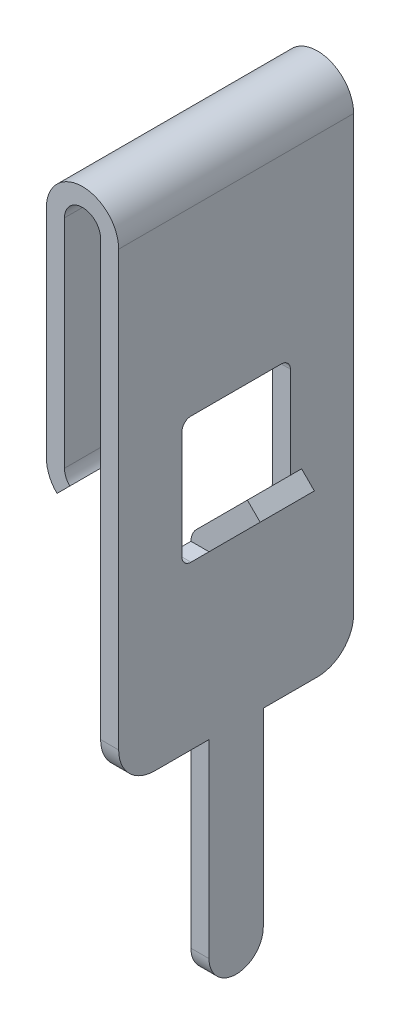
SolidWorks part; units mm, degrees
material "Никель"
ref_plane "Спереди" through (0, 0, 0) normal (0, 0, 1) x (1, 0, 0)
ref_plane "Сверху" through (0, 0, 0) normal (0, 1, 0) x (1, 0, 0)
ref_plane "Справа" through (0, 0, 0) normal (1, 0, 0) x (0, 0, -1)
sketch "Эскиз1" plane through (0, 0, 0) normal (0, 0, 1) x (1, 0, 0)
  line L1 (0, 19) -> (-1, 19) construction
  line L2 (-2, 19) -> (-2, 13)
  line L3 (-2, 13) -> (-1, 13) construction
  line L4 (0, 0) -> (-0.5, 0)
  line L5 (-1, 13) -> (-1.7071, 12.2929) construction
  line L6 (-0.5, 0) -> (-0.5, 19)
  line L7 (-1.5, 19) -> (-1.5, 13)
  line L8 (-1.7071, 12.2929) -> (-1.3536, 12.6464)
  line L9 (0, 0) -> (0, 10.5)
  line L10 (0, 10.5) -> (1.4142, 11.9142)
  line L11 (1.4142, 11.9142) -> (1.0607, 12.2678)
  line L12 (1.0607, 12.2678) -> (0, 11.2071)
  line L13 (0, 11.2071) -> (0, 19)
  arc A0 (0, 19) -> (-2, 19) centre (-1, 19) ccw
  arc A1 (-2, 13) -> (-1.7071, 12.2929) centre (-1, 13) ccw
  arc A2 (-0.5, 19) -> (-1.5, 19) centre (-1, 19) ccw
  arc A3 (-1.5, 13) -> (-1.3536, 12.6464) centre (-1, 13) ccw
extrude "Бобышка-Вытянуть1" add sketch "Эскиз1" along normal blind 6.5
sketch "Эскиз2" plane through (-0.5, 0, 0) normal (-1, 0, 0) x (0, 0, 1)
  line L0 (4, 6) -> (5.5, 6)
  line L2 (6.5, 19) -> (6.5, 0) construction
  line L3 (1, 6) -> (2.5, 6)
  line L4 (2.5, 0.75) -> (2.5, 6)
  line L5 (4, 0.75) -> (4, 6)
  line L6 (0, 19) -> (0, 0) construction
  line L7 (0, 7) -> (-2, 7)
  line L8 (6.5, 7) -> (8.5, 7)
  line L9 (-2, 7) -> (-2, -1)
  line L10 (-2, -1) -> (8.5, -1)
  line L11 (8.5, -1) -> (8.5, 7)
  arc A0 (2.5, 0.75) -> (4, 0.75) centre (3.25, 0.75) ccw
  arc A1 (5.5, 6) -> (6.5, 7) centre (5.5, 7) ccw
  arc A2 (0, 7) -> (1, 6) centre (1, 7) ccw
extrude "Вырез-Вытянуть1" cut sketch "Эскиз2" against normal blind 2
sketch "Эскиз3" plane through (0, 0, 6.5) normal (0, 0, 1) x (1, 0, 0)
  line L0 (0, 10.5) -> (0, 12.5)
  line L1 (0, 11.2071) -> (0, 19) construction
  line L2 (0, 12.5) -> (2, 12.5)
  line L3 (0, 10.5) -> (2, 10.5)
  line L4 (2, 10.5) -> (2, 12.5)
extrude "Вырез-Вытянуть2" cut sketch "Эскиз3" against normal blind 2.5
sketch "Эскиз4" plane through (0, 0, 0) normal (0, 0, -1) x (-1, 0, 0)
  line L0 (0, 10.5) -> (-2, 10.5)
  line L1 (-2, 10.5) -> (-2, 12.5)
  line L2 (-2, 12.5) -> (0, 12.5)
  line L3 (0, 11.2071) -> (0, 19) construction
  line L4 (0, 12.5) -> (0, 10.5)
extrude "Вырез-Вытянуть3" cut sketch "Эскиз4" against normal blind 2.5
sketch "Эскиз5" plane through (0, 0, 0) normal (1, 0, 0) x (0, 0, -1)
  line L0 (-3.25, 0) -> (-3.25, 10.5) construction
  line L1 (-3.25, 10.5) -> (-2, 10.5)
  line L2 (-2, 10.5) -> (-2, 10.75) construction
  line L3 (-1.75, 10.75) -> (-1.75, 13.75)
  line L4 (-3.25, 10.5) -> (-4.5, 10.5)
  line L5 (-4.75, 10.75) -> (-4.75, 13.75)
  line L6 (-2, 14) -> (-4.5, 14)
  arc A0 (-4, 0.75) -> (-2.5, 0.75) centre (-3.25, 0.75) ccw construction
  arc A1 (-2, 10.5) -> (-1.75, 10.75) centre (-2, 10.75) ccw
  arc A2 (-1.75, 13.75) -> (-2, 14) centre (-2, 13.75) ccw
  arc A3 (-4.5, 10.5) -> (-4.75, 10.75) centre (-4.5, 10.75) cw
  arc A4 (-4.75, 13.75) -> (-4.5, 14) centre (-4.5, 13.75) cw
extrude "Вырез-Вытянуть4" cut sketch "Эскиз5" against normal blind 0.6
sketch "Эскиз6" plane through (0, 0, 0) normal (-1, 0, 0) x (0, 0, 1)
  line L0 (2.5, 11.2071) -> (4, 11.2071)
  line L1 (4, 11.2071) -> (4, 10.5)
  line L2 (4, 10.5) -> (2.5, 10.5)
  line L3 (2.5, 10.5) -> (2.5, 11.2071)
extrude "Бобышка-Вытянуть2" add sketch "Эскиз6" along normal blind 0.5
sketch "Эскиз7" plane through (0, 0, 2.5) normal (0, 0, -1) x (-1, 0, 0)
  line L0 (0, 11.2071) -> (0.5, 10.7071)
  line L1 (0.5, 19) -> (0.5, 7) construction
  line L3 (0.5, 10.7071) -> (1, 10.7071)
  line L4 (1, 10.7071) -> (1, 11.2071)
  line L5 (1, 11.2071) -> (0, 11.2071)
extrude "Вырез-Вытянуть5" cut sketch "Эскиз7" against normal blind 2
fillet "Скругление1" radius 0.5 1 edges at (-0.5, 10.7071, 3.25)
